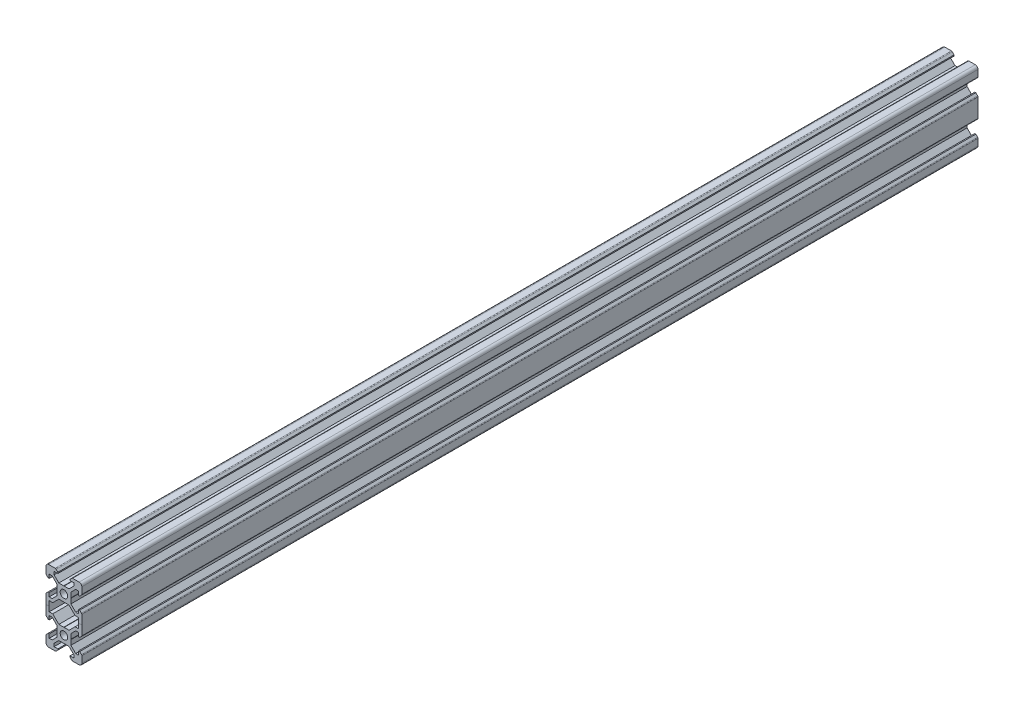
SolidWorks part; units mm, degrees
material "6063-T5"
ref_plane "Front" through (0, 0, 0) normal (0, 0, 1) x (1, 0, 0)
ref_plane "Top" through (0, 0, 0) normal (0, 1, 0) x (1, 0, 0)
ref_plane "Right" through (0, 0, 0) normal (1, 0, 0) x (0, 0, -1)
sketch "Sketch1" plane through (0, 0, 0) normal (0, 0, 1) x (1, 0, 0)
  line L0 (-8.5, 10) -> (-10, 8.5) construction
  line L1 (-8.5, 10) -> (-4.8628, 10)
  line L2 (-10, 8.5) -> (-10, 4.8628)
  line L4 (10, 8.5) -> (10, 4.8628)
  line L5 (-10, 10) -> (10, -10) construction
  line L6 (-10, -10) -> (10, 10) construction
  line L7 (8.2, -5.5) -> (8.2, -3.3865)
  line L8 (-8.2, -5.5) -> (-8.2, -3.3865)
  line L9 (-5.5, 8.2) -> (-3.3865, 8.2)
  line L10 (-8.2, -12.7) -> (-8.2, -7.3)
  line L11 (-3.9005, 2.8395) -> (-6.561, 5.5)
  line L12 (-6.561, 5.5) -> (-8.2, 5.5)
  line L13 (-2.8395, -3.9005) -> (-0.1, -3.9005)
  line L14 (-3.9005, -2.8395) -> (-3.9005, -0.1)
  line L15 (-2.8395, 3.9005) -> (-0.1, 3.9005)
  line L16 (3.9005, -2.8395) -> (3.9005, -0.1)
  line L17 (-8.2, 3.3865) -> (-8.81, 3.3865)
  line L18 (-8.81, 3.3865) -> (-9.7976, 4.3741)
  line L19 (8.5, 10) -> (10, 8.5) construction
  line L20 (-2.8395, 3.9005) -> (-5.5, 6.561)
  line L21 (-5.5, 6.561) -> (-5.5, 8.2)
  line L22 (-3.3865, 8.2) -> (-3.3865, 8.81)
  line L23 (-3.3865, 8.81) -> (-4.3741, 9.7976)
  line L24 (0, 24.069) -> (0, -33.8154) construction
  line L25 (3.3865, 8.81) -> (4.3741, 9.7976)
  line L26 (3.3865, 8.2) -> (3.3865, 8.81)
  line L27 (5.5, 6.561) -> (5.5, 8.2)
  line L28 (2.8395, 3.9005) -> (5.5, 6.561)
  line L29 (3.3865, 8.2) -> (5.5, 8.2)
  line L30 (4.8628, 10) -> (8.5, 10)
  line L31 (-0.1, 3.9005) -> (0, 3.8005)
  line L32 (0.1, 3.9005) -> (0, 3.8005)
  line L33 (0.1, 3.9005) -> (2.8395, 3.9005)
  line L34 (25.9287, 0) -> (-28.3459, 0) construction
  line L35 (-0.1, -3.9005) -> (0, -3.8005)
  line L36 (0.1, -3.9005) -> (0, -3.8005)
  line L37 (0.1, -3.9005) -> (2.8395, -3.9005)
  line L38 (-3.9005, 0.1) -> (-3.8005, 0)
  line L39 (-3.8005, 0) -> (-3.9005, -0.1)
  line L40 (-3.9005, 0.1) -> (-3.9005, 2.8395)
  line L41 (3.9005, 0.1) -> (3.8005, 0)
  line L42 (3.8005, 0) -> (3.9005, -0.1)
  line L43 (3.9005, 0.1) -> (3.9005, 2.8395)
  line L44 (8.81, 3.3865) -> (9.7976, 4.3741)
  line L45 (8.2, 3.3865) -> (8.81, 3.3865)
  line L46 (6.561, 5.5) -> (8.2, 5.5)
  line L47 (3.9005, 2.8395) -> (6.561, 5.5)
  line L48 (2.8395, -3.9005) -> (5.5, -6.561)
  line L49 (3.9005, -2.8395) -> (6.561, -5.5)
  line L50 (-2.8395, -3.9005) -> (-5.5, -6.561)
  line L51 (-3.9005, -2.8395) -> (-6.561, -5.5)
  line L52 (6.561, -5.5) -> (8.2, -5.5)
  line L53 (-6.561, -5.5) -> (-8.2, -5.5)
  line L54 (-8.81, -3.3865) -> (-9.7976, -4.3741)
  line L55 (-8.2, -3.3865) -> (-8.81, -3.3865)
  line L56 (8.81, -3.3865) -> (9.7976, -4.3741)
  line L57 (8.2, -3.3865) -> (8.81, -3.3865)
  line L58 (8.2, 3.3865) -> (8.2, 5.5)
  line L59 (10, -4.8628) -> (10, -15.1372)
  line L60 (-8.2, 3.3865) -> (-8.2, 5.5)
  line L61 (-10, -4.8628) -> (-10, -15.1372)
  line L62 (-28.3459, -10) -> (-10, -10) construction
  line L63 (-3.9005, -20.1) -> (-3.9005, -22.8395)
  line L64 (-3.9005, -20.1) -> (-3.8005, -20)
  line L65 (-3.8005, -20) -> (-3.9005, -19.9)
  line L66 (3.9005, -20.1) -> (3.9005, -22.8395)
  line L67 (3.9005, -20.1) -> (3.8005, -20)
  line L68 (3.8005, -20) -> (3.9005, -19.9)
  line L69 (6.561, -14.5) -> (8.2, -14.5)
  line L70 (3.9005, -17.1605) -> (6.561, -14.5)
  line L71 (3.9005, -17.1605) -> (3.9005, -19.9)
  line L72 (-3.9005, -17.1605) -> (-3.9005, -19.9)
  line L73 (-3.9005, -17.1605) -> (-6.561, -14.5)
  line L74 (-6.561, -14.5) -> (-8.2, -14.5)
  line L75 (-8.2, -16.6135) -> (-8.81, -16.6135)
  line L76 (-8.81, -16.6135) -> (-9.7976, -15.6259)
  line L77 (8.2, -16.6135) -> (8.81, -16.6135)
  line L78 (8.81, -16.6135) -> (9.7976, -15.6259)
  line L79 (-2.8395, -16.0995) -> (-5.5, -13.439)
  line L80 (-2.8395, -16.0995) -> (-0.1, -16.0995)
  line L81 (-0.1, -16.0995) -> (0, -16.1995)
  line L82 (0.1, -16.0995) -> (0, -16.1995)
  line L83 (0.1, -16.0995) -> (2.8395, -16.0995)
  line L84 (2.8395, -16.0995) -> (5.5, -13.439)
  line L85 (-8.2, -16.6135) -> (-8.2, -14.5)
  line L86 (8.2, -16.6135) -> (8.2, -14.5)
  line L87 (2.8395, -23.9005) -> (5.5, -26.561)
  line L88 (-2.8395, -23.9005) -> (-5.5, -26.561)
  line L89 (-0.1, -23.9005) -> (0, -23.8005)
  line L90 (0.1, -23.9005) -> (0, -23.8005)
  line L91 (0.1, -23.9005) -> (2.8395, -23.9005)
  line L92 (-2.8395, -23.9005) -> (-0.1, -23.9005)
  line L93 (-10, -28.5) -> (-10, -24.8628)
  line L94 (10, -28.5) -> (10, -24.8628)
  line L95 (8.81, -23.3865) -> (9.7976, -24.3741)
  line L96 (-8.81, -23.3865) -> (-9.7976, -24.3741)
  line L97 (-8.2, -23.3865) -> (-8.81, -23.3865)
  line L98 (8.2, -23.3865) -> (8.81, -23.3865)
  line L99 (8.2, -23.3865) -> (8.2, -25.5)
  line L100 (-8.2, -23.3865) -> (-8.2, -25.5)
  line L101 (-6.561, -25.5) -> (-8.2, -25.5)
  line L102 (6.561, -25.5) -> (8.2, -25.5)
  line L103 (3.9005, -22.8395) -> (6.561, -25.5)
  line L104 (-3.9005, -22.8395) -> (-6.561, -25.5)
  line L105 (-5.5, -28.2) -> (-3.3865, -28.2)
  line L106 (3.3865, -28.2) -> (5.5, -28.2)
  line L107 (3.3865, -28.2) -> (3.3865, -28.81)
  line L108 (3.3865, -28.81) -> (4.3741, -29.7976)
  line L109 (-3.3865, -28.2) -> (-3.3865, -28.81)
  line L110 (-3.3865, -28.81) -> (-4.3741, -29.7976)
  line L111 (-8.5, -30) -> (-4.8628, -30)
  line L112 (4.8628, -30) -> (8.5, -30)
  line L113 (-5.5, -26.561) -> (-5.5, -28.2)
  line L114 (5.5, -26.561) -> (5.5, -28.2)
  line L115 (-6.239, -7.3) -> (-8.2, -7.3)
  line L116 (-5.5, -6.561) -> (-6.239, -7.3)
  line L117 (6.239, -7.3) -> (8.2, -7.3)
  line L118 (5.5, -6.561) -> (6.239, -7.3)
  line L119 (-6.239, -12.7) -> (-8.2, -12.7)
  line L120 (-5.5, -13.439) -> (-6.239, -12.7)
  line L121 (5.5, -13.439) -> (6.239, -12.7)
  line L122 (6.239, -12.7) -> (8.2, -12.7)
  line L123 (8.2, -12.7) -> (8.2, -7.3)
  line L125 (10, -10) -> (25.9287, -10) construction
  circle A0 centre (0, 0) radius 2.1
  arc A1 (-8.5, 10) -> (-10, 8.5) centre (-8.5, 8.5) ccw
  arc A2 (10, 8.5) -> (8.5, 10) centre (8.5, 8.5) ccw
  arc A3 (-4.3741, 9.7976) -> (-4.8628, 10) centre (-4.8628, 9.3088) ccw
  arc A4 (4.8628, 10) -> (4.3741, 9.7976) centre (4.8628, 9.3088) ccw
  circle A5 centre (0, -20) radius 2.1
  arc A6 (9.7976, 4.3741) -> (10, 4.8628) centre (9.3088, 4.8628) ccw
  arc A7 (-10, 4.8628) -> (-9.7976, 4.3741) centre (-9.3088, 4.8628) ccw
  arc A8 (-10, -4.8628) -> (-9.7976, -4.3741) centre (-9.3088, -4.8628) cw
  arc A9 (9.7976, -4.3741) -> (10, -4.8628) centre (9.3088, -4.8628) cw
  arc A10 (-10, -15.1372) -> (-9.7976, -15.6259) centre (-9.3088, -15.1372) ccw
  arc A11 (9.7976, -15.6259) -> (10, -15.1372) centre (9.3088, -15.1372) ccw
  arc A12 (-10, -24.8628) -> (-9.7976, -24.3741) centre (-9.3088, -24.8628) cw
  arc A13 (9.7976, -24.3741) -> (10, -24.8628) centre (9.3088, -24.8628) cw
  arc A14 (4.8628, -30) -> (4.3741, -29.7976) centre (4.8628, -29.3088) cw
  arc A15 (-4.3741, -29.7976) -> (-4.8628, -30) centre (-4.8628, -29.3088) cw
  arc A16 (-8.5, -30) -> (-10, -28.5) centre (-8.5, -28.5) cw
  arc A17 (10, -28.5) -> (8.5, -30) centre (8.5, -28.5) cw
  point P17 (-9.25, 9.25)
  point P21 (9.25, 9.25)
  dimension "D2" = 4.2
  dimension "D4" = 1.5
  dimension "D3" = 20
  dimension "D5" = 0.529
  dimension "D6" = 6.773
  dimension "D7" = 90
  dimension "D8" = 11
  dimension "D9" = 0.61
  dimension "D10" = 0.1
  dimension "D11" = 0.1
  dimension "D12" = 0.1
  dimension "D13" = 0.1
  dimension "D14" = 5.679
  dimension "D15" = 1.639
  dimension "D16" = 1.8
  dimension "D17" = 90
  dimension "D18" = 6.773
  dimension "D19" = 90
  dimension "D20" = 20
  dimension "D21" = 1.8
extrude "Boss-Extrude2" add sketch "Sketch1" along normal blind 500
sketch "Sketch2" plane through (0, 0, 0) normal (0, 0, -1) x (-1, 0, 0)
  line L0 (-10, -10) -> (10, -10)
  line L1 (-10, -15.1372) -> (-10, -4.8628) construction
  line L2 (10, -4.8628) -> (10, -15.1372) construction
split line "SideFixture1 - SplitLine"
sketch "Sketch3" plane through (0, 0, 500) normal (0, 0, 1) x (1, 0, 0)
  line L0 (-10, -10) -> (10, -10)
  line L1 (-10, -4.8628) -> (-10, -15.1372) construction
  line L2 (10, -15.1372) -> (10, -4.8628) construction
split line "SideFixture2 - SplitLine"
sketch "Sketch4" plane through (0, 10, 0) normal (0, 1, 0) x (1, 0, 0)
  line L0 (-8.5, -250) -> (8.5, -250)
  line L1 (-8.5, -500) -> (-8.5, 0) construction
  line L2 (8.5, -500) -> (8.5, 0) construction
split line "SideFixture3 - SplitLine"
